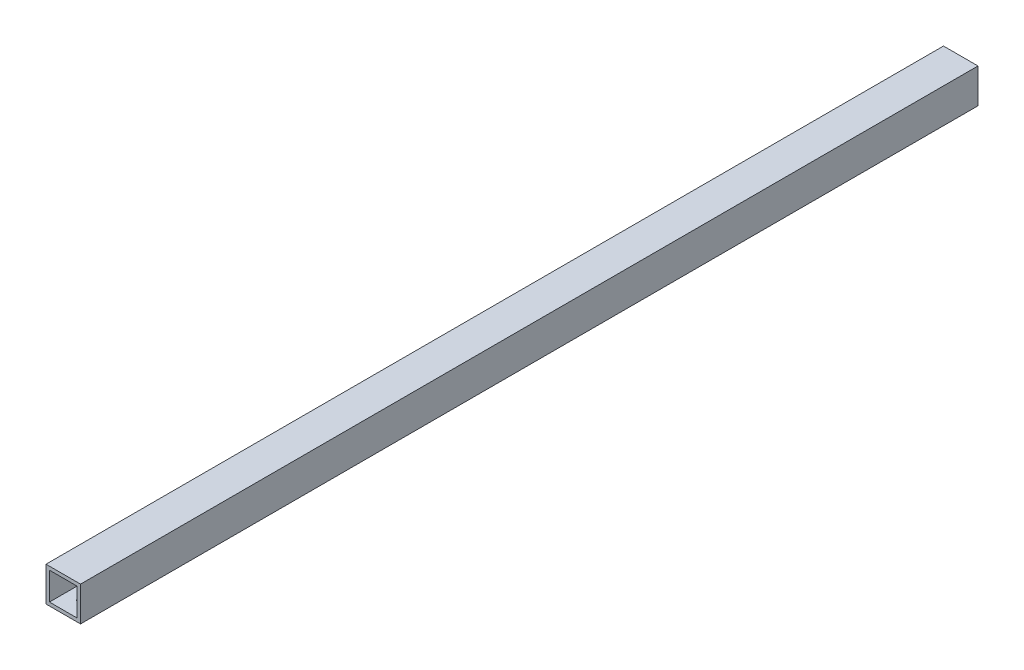
SolidWorks part; units mm, degrees
ref_plane "正面" through (0, 0, 0) normal (0, 0, 1) x (1, 0, 0)
ref_plane "平面" through (0, 0, 0) normal (0, 1, 0) x (1, 0, 0)
ref_plane "右側面" through (0, 0, 0) normal (1, 0, 0) x (0, 0, -1)
sketch "ｽｹｯﾁ1" plane through (0, 0, 0) normal (0, 0, 1) x (1, 0, 0)
  line L1 (-10, 10) -> (10, 10)
  line L2 (-10, 10) -> (-10, -10)
  line L3 (-10, -10) -> (10, -10)
  line L4 (10, 10) -> (10, -10)
  line L5 (-10, 10) -> (10, -10) construction
  line L6 (-10, -10) -> (10, 10) construction
  line L7 (-8, 8) -> (8, 8)
  line L8 (-8, 8) -> (-8, -8)
  line L9 (-8, -8) -> (8, -8)
  line L10 (8, 8) -> (8, -8)
  line L11 (-8, 8) -> (8, -8) construction
  line L12 (-8, -8) -> (8, 8) construction
  point P0 (0, 0)
  point P6 (0, 0)
  dimension "D1" = 20
  dimension "D2" = 20
  dimension "D3" = 16
  dimension "D4" = 16
extrude "ﾎﾞｽ - 押し出し1" add sketch "ｽｹｯﾁ1" along normal blind 560
sketch "ｽｹｯﾁ3" plane through (10, 0, 0) normal (1, 0, 0) x (0, 0, -1)
  line L0 (-560, 0) -> (-530, 0)
  line L1 (-560, -10) -> (-560, 10) construction
  line L2 (-530, 0) -> (-30, 0)
  circle A0 centre (-530, 0) radius 2.2
  circle A1 centre (-30, 0) radius 2.2
  dimension "D2" = 4.4
  dimension "D4" = 4.4
  dimension "D1" = 30
  dimension "D3" = 500
sketch "ｽｹｯﾁ4" plane through (0, 10, 0) normal (0, 1, 0) x (1, 0, 0)
  line L0 (0, -560) -> (0, -550)
  line L1 (10, -560) -> (-10, -560) construction
  line L2 (0, -550) -> (0, -10)
  circle A0 centre (0, -550) radius 2.2
  circle A1 centre (0, -10) radius 2.2
  dimension "D2" = 4.4
  dimension "D4" = 4.4
  dimension "D1" = 10
  dimension "D3" = 540
extrude "ｶｯﾄ - 押し出し3" cut sketch "ｽｹｯﾁ4" against normal blind 560
sketch "ｽｹｯﾁ5" plane through (0, 0, 0) normal (0, 0, -1) x (-1, 0, 0)
  line L0 (10, 10) -> (10, -10) construction
  line L1 (-10, -10) -> (10, -10)
  line L2 (-10, -10) -> (-10, 10)
  line L3 (-10, 10) -> (10, 10)
  line L4 (10, -10) -> (10, 10)
  line L5 (-10, -10) -> (10, 10) construction
  line L6 (-10, 10) -> (10, -10) construction
  line L8 (-8, -8) -> (8, -8)
  line L9 (-8, -8) -> (-8, 8)
  line L10 (-8, 8) -> (8, 8)
  line L11 (8, -8) -> (8, 8)
  line L12 (-8, -8) -> (8, 8) construction
  line L13 (-8, 8) -> (8, -8) construction
  point P1 (0, 0)
  point P8 (0, 0)
extrude "ﾎﾞｽ - 押し出し2" add sketch "ｽｹｯﾁ5" along normal blind 20
sketch "ｽｹｯﾁ6" plane through (0, 0, 560) normal (0, 0, 1) x (1, 0, 0)
  line L1 (10, -10) -> (-10, -10)
  line L2 (10, -10) -> (10, 10)
  line L3 (10, 10) -> (-10, 10)
  line L4 (-10, -10) -> (-10, 10)
  line L5 (10, -10) -> (-10, 10) construction
  line L6 (10, 10) -> (-10, -10) construction
  line L7 (8, -8) -> (-8, -8)
  line L8 (8, -8) -> (8, 8)
  line L9 (8, 8) -> (-8, 8)
  line L10 (-8, -8) -> (-8, 8)
  line L11 (8, -8) -> (-8, 8) construction
  line L12 (8, 8) -> (-8, -8) construction
  point P0 (0, 0)
  point P7 (0, 0)
extrude "ﾎﾞｽ - 押し出し3" add sketch "ｽｹｯﾁ6" along normal blind 20
sketch "ｽｹｯﾁ8" plane through (10, 0, 0) normal (1, 0, 0) x (0, 0, -1)
  line L0 (20, 0) -> (10, 0)
  line L1 (20, 10) -> (20, -10) construction
  line L2 (-580, 0) -> (-570, 0)
  line L3 (-580, -10) -> (-580, 10) construction
  circle A0 centre (10, 0) radius 2.2
  circle A1 centre (-570, 0) radius 2.2
  dimension "D2" = 4.4
  dimension "D4" = 4.4
  dimension "D1" = 10
  dimension "D3" = 10
extrude "ｶｯﾄ - 押し出し4" cut sketch "ｽｹｯﾁ8" against normal blind 20 contours A1
sketch "ｽｹｯﾁ9" plane through (10, 0, 0) normal (1, 0, 0) x (0, 0, -1)
  line L0 (20, 0) -> (10, 0)
  line L1 (20, 10) -> (20, -10) construction
  circle A0 centre (10, 0) radius 2.2
  dimension "D2" = 4.4
  dimension "D1" = 10
extrude "ｶｯﾄ - 押し出し5" cut sketch "ｽｹｯﾁ9" against normal blind 20
sketch "ｽｹｯﾁ10" plane through (0, 0, -20) normal (0, 0, -1) x (-1, 0, 0)
  line L1 (25.7112, -15.2204) -> (-25.7112, -15.2204)
  line L2 (25.7112, -15.2204) -> (25.7112, 15.2204)
  line L3 (25.7112, 15.2204) -> (-25.7112, 15.2204)
  line L4 (-25.7112, -15.2204) -> (-25.7112, 15.2204)
  line L5 (25.7112, -15.2204) -> (-25.7112, 15.2204) construction
  line L6 (25.7112, 15.2204) -> (-25.7112, -15.2204) construction
  point P0 (0, 0)
extrude "ｶｯﾄ - 押し出し6" cut sketch "ｽｹｯﾁ10" against normal blind 40
sketch "ｽｹｯﾁ11" plane through (0, 0, 580) normal (0, 0, 1) x (1, 0, 0)
  line L1 (19.6813, -26.3737) -> (-19.6813, -26.3737)
  line L2 (19.6813, -26.3737) -> (19.6813, 26.3737)
  line L3 (19.6813, 26.3737) -> (-19.6813, 26.3737)
  line L4 (-19.6813, -26.3737) -> (-19.6813, 26.3737)
  line L5 (19.6813, -26.3737) -> (-19.6813, 26.3737) construction
  line L6 (19.6813, 26.3737) -> (-19.6813, -26.3737) construction
  point P0 (0, 0)
extrude "ｶｯﾄ - 押し出し7" cut sketch "ｽｹｯﾁ11" against normal blind 40
sketch "ｽｹｯﾁ12" plane through (0, -10, 0) normal (0, -1, 0) x (-1, 0, 0)
  line L0 (0, -540) -> (0, -530)
  line L1 (10, -540) -> (-10, -540) construction
  line L2 (0, -530) -> (0, -510)
  circle A0 centre (0, -530) radius 1
  circle A1 centre (0, -510) radius 1
  dimension "D3" = 2
  dimension "D4" = 2
  dimension "D1" = 10
  dimension "D2" = 20
extrude "ｶｯﾄ - 押し出し8" cut sketch "ｽｹｯﾁ12" against normal blind 10
sketch "ｽｹｯﾁ13" plane through (0, -10, 0) normal (0, -1, 0) x (-1, 0, 0)
  line L0 (0, -20) -> (0, -30)
  line L1 (-10, -20) -> (10, -20) construction
  line L2 (0, -30) -> (0, -50)
  circle A0 centre (0, -30) radius 1
  circle A1 centre (0, -50) radius 1
  dimension "D3" = 2
  dimension "D4" = 2
  dimension "D1" = 10
  dimension "D2" = 20
extrude "ｶｯﾄ - 押し出し9" cut sketch "ｽｹｯﾁ13" against normal blind 10
hole_wizard "M4x0.7 ねじ穴1" positions "3Dｽｹｯﾁ2" profile "ｽｹｯﾁ15" tap size "M4x0.7" standard "JIS"
sketch3d "3Dｽｹｯﾁ2"
  line L0 (0, -8, 30) -> (0, -10, 30) construction
  line L1 (0, -8, 50) -> (0, -10, 50) construction
  line L2 (0, -8, 510) -> (0, -10, 510) construction
  line L3 (0, -8, 530) -> (0, -10, 530) construction
  point P0 (0, -10, 30)
  point P4 (0, -10, 50)
  point P8 (0, -10, 510)
  point P12 (0, -10, 530)
sketch "ｽｹｯﾁ15" plane through (0, -10, 30) normal (1, 0, 0) x (0, 0, -1)
  line L0 (0, 0) -> (0, 12.4914)
  line L1 (0, 12.4914) -> (1.65, 11.5)
  line L2 (1.65, 11.5) -> (1.65, 0)
  line L5 (1.65, 0) -> (0, 0)
  line L10 (0, 12.4914) -> (-1.65, 11.5) construction
  line L11 (0, -6.35) -> (0, 107.95) construction
  dimension "ねじ下穴ﾄﾞﾘﾙ直径" = 3.3
  dimension "ねじ下穴ﾄﾞﾘﾙの深さ" = 11.5
  dimension "ﾄﾞﾘﾙ角度" = 118
cosmetic thread "穴のねじ山1" parameters "D1"=2, "D2"=4
cosmetic thread "穴のねじ山2" parameters "D1"=2, "D2"=4
cosmetic thread "穴のねじ山3" parameters "D1"=2, "D2"=4
cosmetic thread "穴のねじ山4" parameters "D1"=2, "D2"=4
